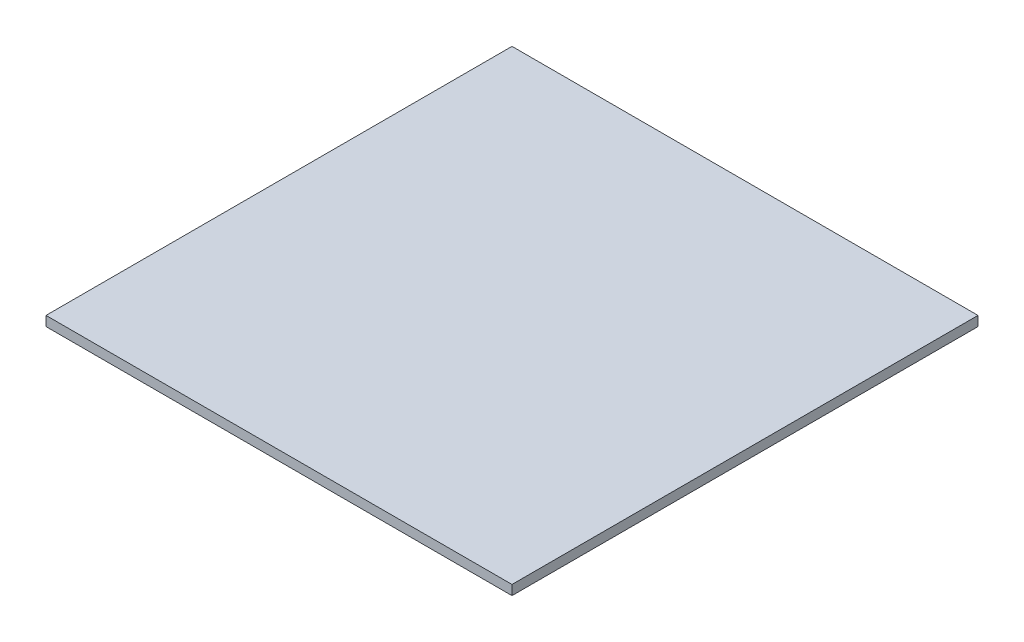
SolidWorks part; units mm, degrees
ref_plane "Front Plane" through (0, 0, 0) normal (0, 0, 1) x (1, 0, 0)
ref_plane "Top Plane" through (0, 0, 0) normal (0, 1, 0) x (1, 0, 0)
ref_plane "Right Plane" through (0, 0, 0) normal (1, 0, 0) x (0, 0, -1)
sketch "Sketch1" plane through (0, 0, 0) normal (0, 1, 0) x (1, 0, 0)
  line L1 (-304.8, -304.8) -> (304.8, -304.8)
  line L2 (-304.8, -304.8) -> (-304.8, 304.8)
  line L3 (-304.8, 304.8) -> (304.8, 304.8)
  line L4 (304.8, -304.8) -> (304.8, 304.8)
  line L5 (-304.8, -304.8) -> (304.8, 304.8) construction
  line L6 (-304.8, 304.8) -> (304.8, -304.8) construction
  point P0 (0, 0)
  dimension "D1" = 609.6
  dimension "D2" = 609.6
extrude "Boss-Extrude1" add sketch "Sketch1" along normal blind 12.7
